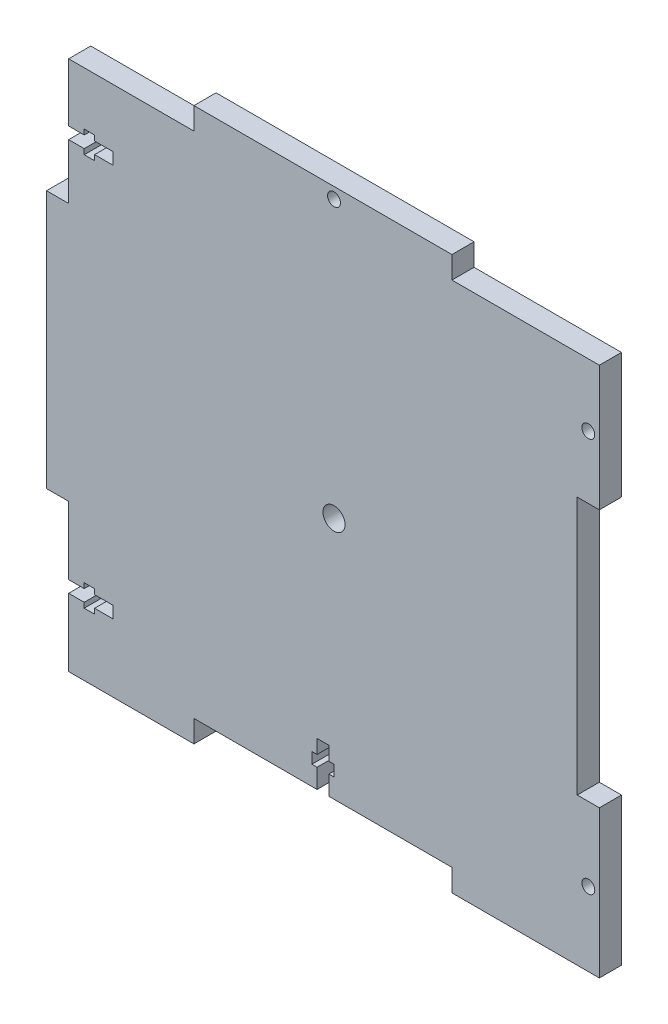
SolidWorks part; units mm, degrees
ref_plane "Front Plane" through (0, 0, 0) normal (0, 0, 1) x (1, 0, 0)
ref_plane "Top Plane" through (0, 0, 0) normal (0, 1, 0) x (1, 0, 0)
ref_plane "Right Plane" through (0, 0, 0) normal (1, 0, 0) x (0, 0, -1)
sketch "Sketch1" plane through (0, 0, 0) normal (0, 0, 1) x (1, 0, 0)
  line L0 (-38, 72) -> (-38, 78)
  line L1 (-72, -72) -> (72, -72)
  line L2 (-72, -72) -> (-72, 72)
  line L3 (-72, 72) -> (72, 72)
  line L4 (72, -72) -> (72, 72)
  line L5 (-72, -72) -> (72, 72) construction
  line L6 (-72, 72) -> (72, -72) construction
  line L7 (-38, 78) -> (32, 78)
  line L8 (32, 78) -> (32, 72)
  line L9 (-38, -72) -> (-38, -66)
  line L10 (-38, -66) -> (32, -66)
  line L11 (32, -66) -> (32, -72)
  line L12 (-72, 38) -> (-78, 38)
  line L13 (-78, 38) -> (-78, -32)
  line L14 (-78, -32) -> (-72, -32)
  line L15 (72, 38) -> (66, 38)
  line L16 (66, 38) -> (66, -32)
  line L17 (66, -32) -> (72, -32)
  line L18 (0, 108.2426) -> (0, -112.6743) construction
  line L19 (-72, 56.2) -> (-60, 56.2)
  line L24 (-72, -50.4) -> (-60, -50.4)
  line L25 (-72, -50.4) -> (-72, -53.6)
  line L26 (-72, -53.6) -> (-60, -53.6)
  line L27 (-60, -50.4) -> (-60, -53.6)
  line L28 (-67.7819, -49) -> (-64.967, -49)
  line L29 (-67.7819, -49) -> (-67.7819, -55)
  line L30 (-67.7819, -55) -> (-64.967, -55)
  line L31 (-64.967, -49) -> (-64.967, -55)
  line L32 (-72, 53) -> (-60, 53)
  line L33 (-60, 56.2) -> (-60, 53)
  line L34 (-67.7728, 57.6) -> (-64.958, 57.6)
  line L35 (-67.7728, 57.6) -> (-67.7728, 51.5685)
  line L36 (-67.7728, 51.5685) -> (-64.958, 51.5685)
  line L37 (-64.958, 57.6) -> (-64.958, 51.5685)
  line L38 (-4.6, -54) -> (-1.4, -54)
  line L39 (-4.6, -54) -> (-4.6, -66)
  line L40 (-4.6, -66) -> (-1.4, -66)
  line L41 (-1.4, -54) -> (-1.4, -66)
  line L42 (-6, -57.7715) -> (0, -57.7715)
  line L43 (-6, -57.7715) -> (-6, -60.7715)
  line L44 (-6, -60.7715) -> (0, -60.7715)
  line L45 (0, -57.7715) -> (0, -60.7715)
  circle A0 centre (69, 55) radius 1.75
  circle A3 centre (69, -52) radius 1.75
  circle A6 centre (0, 75) radius 1.75
  circle A8 centre (0, 0) radius 3
  point P0 (0, 0)
  point P56 (-3.2, -60.888)
  point P57 (-6.1692, -60.7715)
  dimension "D16" = 3.5
  dimension "D20" = 12
  dimension "D19" = 3.2
  dimension "D30" = 3
  dimension "D31" = 3.5
  dimension "D32" = 33.4
  dimension "D2" = 6
  dimension "D3" = 40
  dimension "D4" = 40
  dimension "D5" = 6
  dimension "D6" = 40
  dimension "D7" = 150
  dimension "D8" = 6
  dimension "D9" = 6
  dimension "D10" = 40
  dimension "D11" = 40
  dimension "D12" = 6
  dimension "D13" = 40
  dimension "D14" = 40
  dimension "D15" = 150
  dimension "D17" = 3
  dimension "D18" = 17
  dimension "D21" = 18.4
  dimension "D22" = 3
  dimension "D23" = 6
  dimension "D24" = 20
  dimension "D25" = 1.4
  dimension "D26" = 15
  dimension "D27" = 1.4
  dimension "D28" = 3.2
  dimension "D29" = 12
  dimension "D33" = 3
  dimension "D34" = 1.4
  dimension "D35" = 1.4
  dimension "D36" = 3.2
  dimension "D37" = 12
  dimension "D38" = 33.4
  dimension "D39" = 0
extrude "Boss-Extrude2" add sketch "Sketch1" along normal blind 6 contours L17 L16 L15 L4 L3 L2 L1 L9 L10 L11 | L13 L14 L2 L12 | L8 L7 L0 L3
